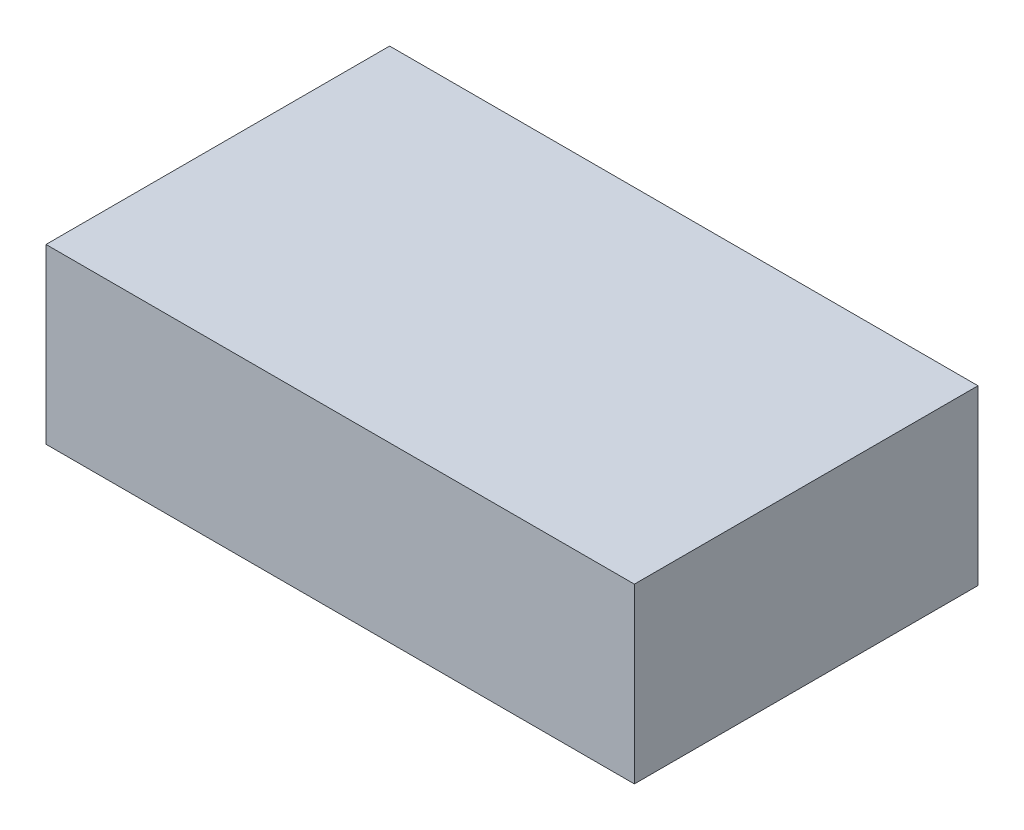
SolidWorks part; units mm, degrees
ref_plane "Front Plane" through (0, 0, 0) normal (0, 0, 1) x (1, 0, 0)
ref_plane "Top Plane" through (0, 0, 0) normal (0, 1, 0) x (1, 0, 0)
ref_plane "Right Plane" through (0, 0, 0) normal (1, 0, 0) x (0, 0, -1)
sketch "Sketch1" plane through (0, 0, 0) normal (0, 1, 0) x (1, 0, 0)
  line L1 (0, 0) -> (238, 0)
  line L2 (0, 0) -> (0, 139)
  line L3 (0, 139) -> (238, 139)
  line L4 (238, 0) -> (238, 139)
  dimension "D1" = 238
  dimension "D2" = 139
extrude "Boss-Extrude1" add sketch "Sketch1" along normal blind 70
